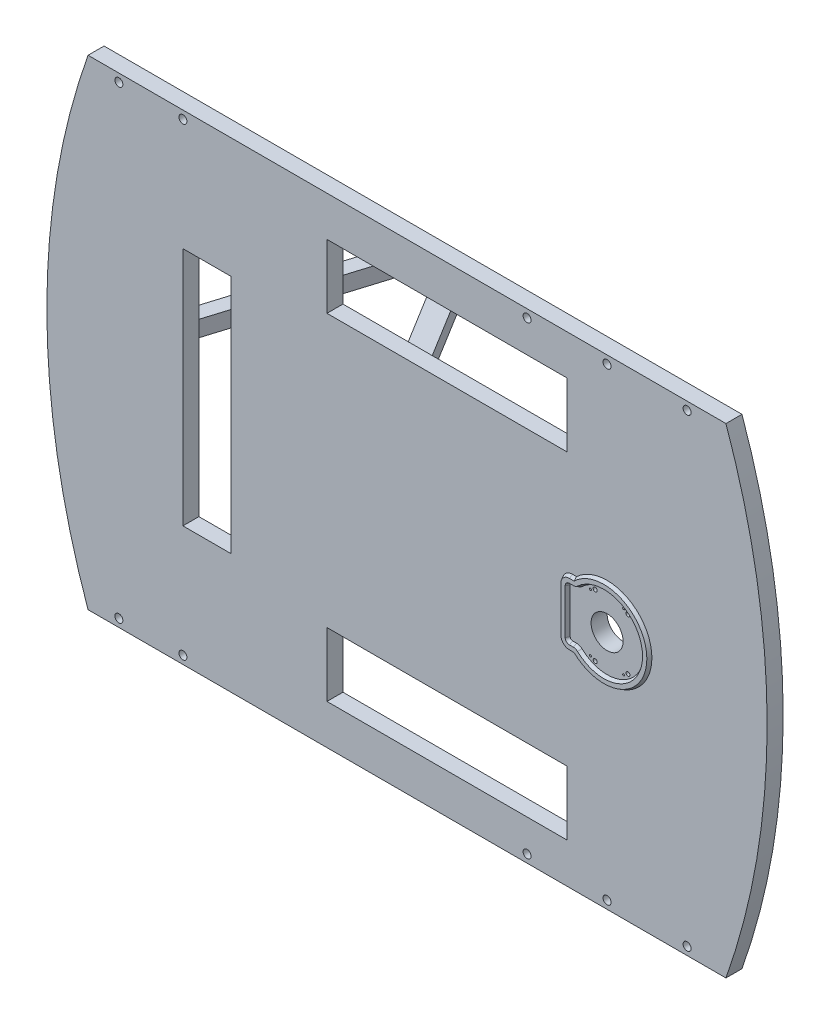
SolidWorks part; units mm, degrees
ref_plane "前视基准面" through (0, 0, 0) normal (0, 0, 1) x (1, 0, 0)
ref_plane "上视基准面" through (0, 0, 0) normal (0, 1, 0) x (1, 0, 0)
ref_plane "右视基准面" through (0, 0, 0) normal (1, 0, 0) x (0, 0, -1)
sketch "草图1" plane through (0, 0, 0) normal (0, 0, 1) x (1, 0, 0)
  line L1 (-700, 300) -> (200, 300)
  line L2 (-700, 300) -> (-700, -300)
  line L3 (-700, -300) -> (200, -300)
  line L4 (200, 300) -> (200, -300)
  dimension "D1" = 300
  dimension "D2" = 300
  dimension "D3" = 200
  dimension "D4" = 700
extrude "凸台-拉伸1" add sketch "草图1" against normal blind 20
sketch "草图2" plane through (0, 0, 0) normal (0, 0, 1) x (1, 0, 0)
  line L0 (-700, -300) -> (200, -300) construction
  line L1 (-746.2577, 1100) -> (454.6203, 1100)
  line L2 (-746.2577, 1100) -> (-746.2577, -900)
  line L3 (-746.2577, -900) -> (454.6203, -900)
  line L4 (454.6203, 1100) -> (454.6203, -900)
  arc A0 (-250, -779.4229) -> (-250, 779.4229) centre (-700, 0) ccw
  arc A1 (-250, 779.4229) -> (-250, -779.4229) centre (200, 0) ccw
  dimension "D2" = 1800
  dimension "D3" = 1800
  dimension "D1" = 700
  dimension "D4" = 200
  dimension "D5" = 2000
  dimension "D6" = 600
extrude "切除-拉伸1" cut sketch "草图2" against normal blind 20
sketch "草图3" plane through (0, 0, 0) normal (0, 0, 1) x (1, 0, 0)
  line L0 (-46.05, 28) -> (-46.05, -28)
  line L1 (-43.05, 31) -> (-38.1445, 31)
  line L2 (-43.05, -31) -> (-38.1445, -31)
  line L3 (-56.05, 28) -> (-56.05, -28)
  line L4 (-43.05, -41) -> (-38.1445, -41)
  line L5 (-43.05, 41) -> (-38.1445, 41)
  arc A0 (-31.333, -33.6786) -> (-31.333, 33.6786) centre (0, 0) ccw
  arc A1 (-46.05, -28) -> (-43.05, -31) centre (-43.05, -28) ccw
  arc A2 (-46.05, 28) -> (-43.05, 31) centre (-43.05, 28) cw
  arc A3 (-38.1445, -31) -> (-31.333, -33.6786) centre (-38.1445, -41) cw
  arc A4 (-38.1445, 31) -> (-31.333, 33.6786) centre (-38.1445, 41) ccw
  arc A5 (-56.05, -28) -> (-43.05, -41) centre (-43.05, -28) ccw
  arc A6 (-38.1445, -41) -> (-38.1445, -41) centre (-38.1445, -41) cw
  arc A7 (-38.1445, -41) -> (-38.1445, 41) centre (0, 0) ccw
  arc A8 (-38.1445, 41) -> (-38.1445, 41) centre (-38.1445, 41) ccw
  arc A9 (-56.05, 28) -> (-43.05, 41) centre (-43.05, 28) cw
  dimension "D1" = 92
  dimension "D5" = 3
  dimension "D6" = 10
  dimension "D2" = 46.05
  dimension "D3" = 31
  dimension "D4" = 31
  dimension "D7" = 10
extrude "凸台-拉伸2" add sketch "草图3" along normal blind 4 draft 30 separate body
sketch "草图4" plane through (0, 0, 0) normal (0, 0, 1) x (1, 0, 0)
  line L0 (0, 0) -> (58.874, 0) construction
  line L1 (26.1168, 32.2516) -> (0, 0) construction
  line L2 (0, 0) -> (20.75, 35.9401) construction
  line L3 (-14.8723, 38.7436) -> (0, 0) construction
  line L4 (0, 0) -> (-20.75, 35.9401) construction
  circle A0 centre (26.1168, 32.2516) radius 2.5
  circle A1 centre (20.75, 35.9401) radius 1.25
  circle A2 centre (-14.8723, 38.7436) radius 2.5
  circle A3 centre (-20.75, 35.9401) radius 1.25
  dimension "D1" = 5
  dimension "D2" = 2.5
  dimension "D3" = 5
  dimension "D4" = 2.5
  dimension "D5" = 41.5
  dimension "D6" = 9
  dimension "D7" = 51
  dimension "D8" = 51
  dimension "D9" = 9
extrude "切除-拉伸2" cut sketch "草图4" against normal blind 15
mirror "镜向1" about plane through (0, 0, 0) normal (0, 1, 0) of "切除-拉伸2"
sketch "草图5" plane through (0, 0, 0) normal (0, 0, 1) x (1, 0, 0)
  line L0 (148.5281, 300) -> (-648.5281, 300) construction
  line L1 (-350, 250) -> (-50, 250)
  line L2 (-350, 250) -> (-350, 170)
  line L3 (-350, 170) -> (-50, 170)
  line L4 (-50, 250) -> (-50, 170)
  line L5 (-350, -170) -> (-50, -170)
  line L6 (-350, -170) -> (-350, -250)
  line L7 (-350, -250) -> (-50, -250)
  line L8 (-50, -170) -> (-50, -250)
  line L9 (-530, 150) -> (-470, 150)
  line L10 (-530, 150) -> (-530, -150)
  line L11 (-530, -150) -> (-470, -150)
  line L12 (-470, 150) -> (-470, -150)
  line L13 (-648.5281, -300) -> (148.5281, -300) construction
  circle A0 centre (0, 0) radius 20
  dimension "D14" = 40
  dimension "D1" = 80
  dimension "D2" = 300
  dimension "D3" = 300
  dimension "D4" = 50
  dimension "D5" = 80
  dimension "D6" = 50
  dimension "D7" = 50
  dimension "D8" = 50
  dimension "D9" = 60
  dimension "D10" = 300
  dimension "D11" = 150
  dimension "D12" = 470
extrude "切除-拉伸3" cut sketch "草图5" against normal through all
sketch "草图6" plane through (0, 0, 0) normal (0, 1, 0) x (1, 0, 0)
  line L0 (-620, 20) -> (-600, 20)
  line L1 (-600, 20) -> (-526.1538, 260)
  line L2 (-526.1538, 260) -> (-477.6923, 260)
  line L3 (-477.6923, 260) -> (-330, 20)
  line L4 (-330, 20) -> (-300, 20)
  line L5 (-300, 20) -> (-460, 280)
  line L6 (-460, 280) -> (-540, 280)
  line L7 (-540, 280) -> (-620, 20)
  line L8 (-648.5281, 0) -> (148.5281, 0) construction
  line L9 (-648.5281, 20) -> (148.5281, 20) construction
  dimension "D1" = 20
  dimension "D2" = 30
  dimension "D3" = 20
  dimension "D4" = 260
  dimension "D5" = 20
  dimension "D6" = 20
  dimension "D7" = 460
  dimension "D8" = 80
  dimension "D9" = 600
  dimension "D10" = 300
extrude "凸台-拉伸3" add sketch "草图6" along normal blind 10 and the other way blind 10 separate body
sketch "草图7" plane through (0, 0, -260) normal (0, 0, 1) x (1, 0, 0)
  line L0 (-526.1538, 10) -> (-477.6923, 10) construction
  line L1 (-477.6923, -10) -> (-477.6923, 10) construction
  line L2 (-526.1538, -10) -> (-526.1538, 10) construction
  circle A0 centre (-516.1538, 0) radius 5
  circle A1 centre (-487.6923, 0) radius 5
  dimension "D1" = 10
  dimension "D2" = 10
  dimension "D3" = 10
  dimension "D4" = 10
  dimension "D5" = 10
  dimension "D6" = 10
extrude "切除-拉伸4" cut sketch "草图7" against normal through all
sketch "草图8" plane through (0, 0, 0) normal (0, 0, 1) x (1, 0, 0)
  line L1 (148.5281, 300) -> (-648.5281, 300) construction
  circle A5 centre (0, 290) radius 5
  circle A6 centre (100, 290) radius 5
  circle A7 centre (-100, 290) radius 5
  circle A8 centre (-610, 290) radius 5
  circle A9 centre (-530, 290) radius 5
  dimension "D1" = 10
  dimension "D6" = 10
  dimension "D2" = 10
  dimension "D3" = 290
  dimension "D5" = 100
  dimension "D7" = 10
  dimension "D4" = 100
  dimension "D8" = 10
  dimension "D9" = 10
  dimension "D10" = 530
  dimension "D11" = 610
extrude "切除-拉伸5" cut sketch "草图8" against normal through all
mirror "镜向2" about plane through (0, 0, 0) normal (0, 1, 0) of "切除-拉伸5"
